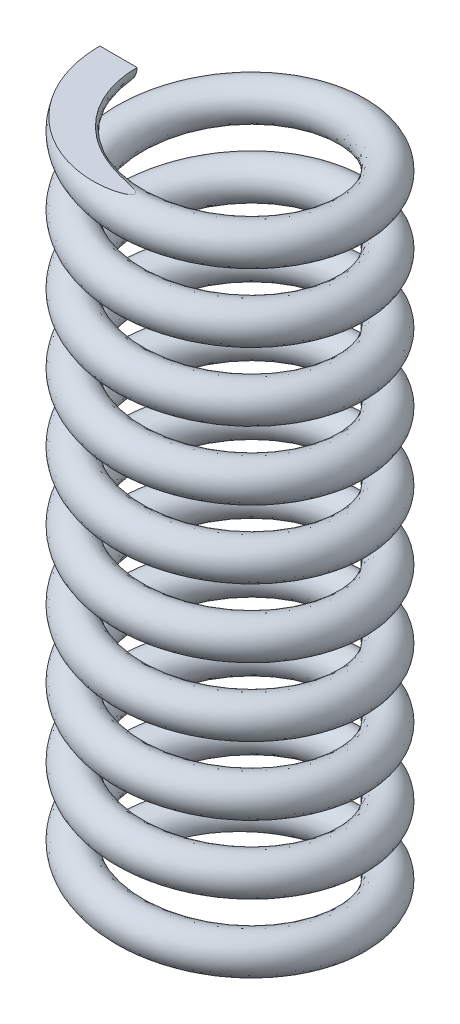
SolidWorks part; units mm, degrees
ref_plane "Front Plane" through (0, 0, 0) normal (0, 0, 1) x (1, 0, 0)
ref_plane "Top Plane" through (0, 0, 0) normal (0, 1, 0) x (1, 0, 0)
ref_plane "Right Plane" through (0, 0, 0) normal (1, 0, 0) x (0, 0, -1)
sketch "Sketch3" plane through (0, 0, 0) normal (0, 1, 0) x (1, 0, 0)
  circle A0 centre (0, 0) radius 30
  dimension "D1" = 60
curve "Helix/Spiral1" pitch 18.3642 height 183.642 turns 10
sketch "Sketch4" plane through (0, 0, 0) normal (0, 0, 1) x (1, 0, 0)
  circle A0 centre (-30, 0) radius 5
  spline S0 degree 3 poles (-30, 0) (-30, 0.2512) (-29.3277, 0.7561) (-26.3694, 1.5114) (-21.6579, 2.2672) (-15.5065, 3.0229) (-8.3241, 3.7786) (-0.5883, 4.5344) (7.1867, 5.2901) (14.4838, 6.0458) (20.8179, 6.8016) (25.768, 7.5573) (29.0049, 8.313) (30.3133, 9.0687) (29.6064, 9.8245) (26.9311, 10.5802) (22.4653, 11.3359) (16.5058, 12.0917) (9.449, 12.8474) (1.7639, 13.6031) (-6.0384, 14.3588) (-13.4393, 15.1146) (-19.9467, 15.8703) (-25.1279, 16.626) (-28.6384, 17.3818) (-30.2449, 18.1375) (-29.8406, 18.8932) (-27.4523, 19.6489) (-23.2388, 20.4047) (-17.4803, 21.1604) (-10.5596, 21.9161) (-2.9369, 22.6719) (4.8811, 23.4276) (12.3746, 24.1833) (19.0454, 24.939) (24.4499, 25.6948) (28.2289, 26.4505) (30.131, 27.2062) (30.0299, 27.962) (27.9322, 28.7177) (23.9775, 29.4734) (18.4286, 30.2291) (11.6544, 30.9849) (4.1054, 31.7406) (-3.7165, 32.4963) (-11.2914, 33.252) (-18.1155, 34.0078) (-23.7352, 34.7635) (-27.7769, 35.5192) (-29.9718, 36.275) (-30.174, 37.0307) (-28.3701, 37.7864) (-24.68, 38.5421) (-19.3491, 39.2979) (-12.7317, 40.0536) (-5.2678, 40.8093) (2.5463, 41.5651) (10.1911, 42.3208) (17.1583, 43.0765) (22.9848, 43.8322) (27.2831, 44.588) (29.7675, 45.3437) (30.2728, 46.0994) (28.7654, 46.8552) (25.3455, 47.6109) (20.2405, 48.3666) (13.7898, 49.1223) (6.4223, 49.8781) (-1.3722, 50.6338) (-9.0755, 51.3895) (-16.1754, 52.1453) (-22.1998, 52.901) (-26.7483, 53.6567) (-29.5184, 54.4124) (-30.326, 55.1682) (-29.1173, 55.9239) (-25.9728, 56.6796) (-21.1015, 57.4354) (-14.8272, 58.1911) (-7.5671, 58.9468) (0.1961, 59.7025) (7.9462, 60.4583) (15.1681, 61.214) (21.3815, 61.9697) (26.1733, 62.7255) (29.225, 63.4812) (30.3336, 64.2369) (29.4255, 64.9926) (26.5611, 65.7484) (21.9307, 66.5041) (15.8422, 67.2598) (8.7005, 68.0156) (0.9803, 68.7713) (-6.805, 69.527) (-14.138, 70.2827) (-20.5309, 71.0385) (-25.5589, 71.7942) (-28.8875, 72.5499) (-30.2956, 73.3057) (-29.6894, 74.0614) (-27.1094, 74.8171) (-22.7269, 75.5728) (-16.8335, 76.3286) (-9.8208, 77.0843) (-2.1553, 77.84) (5.6536, 78.5958) (13.0866, 79.3515) (19.6495, 80.1072) (24.906, 80.8629) (28.5067, 81.6187) (30.212, 82.3744) (29.9087, 83.1301) (27.6169, 83.8859) (23.489, 84.6416) (17.7994, 85.3973) (10.9264, 86.153) (3.327, 86.9088) (-4.4937, 87.6645) (-12.0155, 88.4202) (-18.7385, 89.176) (-24.2157, 89.9317) (-28.0829, 90.6874) (-30.083, 91.4431) (-30.083, 92.1989) (-28.0829, 92.9546) (-24.2157, 93.7103) (-18.7385, 94.466) (-12.0155, 95.2218) (-4.4937, 95.9775) (3.327, 96.7332) (10.9264, 97.489) (17.7994, 98.2447) (23.489, 99.0004) (27.6169, 99.7561) (29.9087, 100.5119) (30.212, 101.2676) (28.5067, 102.0233) (24.906, 102.7791) (19.6495, 103.5348) (13.0866, 104.2905) (5.6536, 105.0462) (-2.1553, 105.802) (-9.8208, 106.5577) (-16.8335, 107.3134) (-22.7269, 108.0692) (-27.1094, 108.8249) (-29.6894, 109.5806) (-30.2956, 110.3363) (-28.8875, 111.0921) (-25.5589, 111.8478) (-20.5309, 112.6035) (-14.138, 113.3593) (-6.805, 114.115) (0.9803, 114.8707) (8.7005, 115.6264) (15.8422, 116.3822) (21.9307, 117.1379) (26.5611, 117.8936) (29.4255, 118.6494) (30.3336, 119.4051) (29.225, 120.1608) (26.1733, 120.9165) (21.3815, 121.6723) (15.1681, 122.428) (7.9462, 123.1837) (0.1961, 123.9395) (-7.5671, 124.6952) (-14.8272, 125.4509) (-21.1015, 126.2066) (-25.9728, 126.9624) (-29.1173, 127.7181) (-30.326, 128.4738) (-29.5184, 129.2296) (-26.7483, 129.9853) (-22.1998, 130.741) (-16.1754, 131.4967) (-9.0755, 132.2525) (-1.3722, 133.0082) (6.4223, 133.7639) (13.7898, 134.5197) (20.2405, 135.2754) (25.3455, 136.0311) (28.7654, 136.7868) (30.2728, 137.5426) (29.7675, 138.2983) (27.2831, 139.054) (22.9848, 139.8098) (17.1583, 140.5655) (10.1911, 141.3212) (2.5463, 142.0769) (-5.2678, 142.8327) (-12.7317, 143.5884) (-19.3491, 144.3441) (-24.68, 145.0999) (-28.3701, 145.8556) (-30.174, 146.6113) (-29.9718, 147.367) (-27.7769, 148.1228) (-23.7352, 148.8785) (-18.1155, 149.6342) (-11.2914, 150.39) (-3.7165, 151.1457) (4.1054, 151.9014) (11.6544, 152.6571) (18.4286, 153.4129) (23.9775, 154.1686) (27.9322, 154.9243) (30.0299, 155.68) (30.131, 156.4358) (28.2289, 157.1915) (24.4499, 157.9472) (19.0454, 158.703) (12.3746, 159.4587) (4.8811, 160.2144) (-2.9369, 160.9701) (-10.5596, 161.7259) (-17.4803, 162.4816) (-23.2388, 163.2373) (-27.4523, 163.9931) (-29.8406, 164.7488) (-30.2449, 165.5045) (-28.6384, 166.2602) (-25.1279, 167.016) (-19.9467, 167.7717) (-13.4393, 168.5274) (-6.0384, 169.2832) (1.7639, 170.0389) (9.449, 170.7946) (16.5058, 171.5503) (22.4653, 172.3061) (26.9311, 173.0618) (29.6064, 173.8175) (30.3133, 174.5733) (29.0049, 175.329) (25.768, 176.0847) (20.8179, 176.8404) (14.4838, 177.5962) (7.1867, 178.3519) (-0.5883, 179.1076) (-8.3241, 179.8634) (-15.5065, 180.6191) (-21.6579, 181.3748) (-26.3694, 182.1306) (-29.3277, 182.8859) (-30, 183.3908) (-30, 183.642) knots 0 0 0 0 0.004115 0.00823 0.012346 0.016461 0.020576 0.024691 0.028807 0.032922 0.037037 0.041152 0.045267 0.049383 0.053498 0.057613 0.061728 0.065844 0.069959 0.074074 0.078189 0.082305 0.08642 0.090535 0.09465 0.098765 0.102881 0.106996 0.111111 0.115226 0.119342 0.123457 0.127572 0.131687 0.135802 0.139918 0.144033 0.148148 0.152263 0.156379 0.160494 0.164609 0.168724 0.17284 0.176955 0.18107 0.185185 0.1893 0.193416 0.197531 0.201646 0.205761 0.209877 0.213992 0.218107 0.222222 0.226337 0.230453 0.234568 0.238683 0.242798 0.246914 0.251029 0.255144 0.259259 0.263374 0.26749 0.271605 0.27572 0.279835 0.283951 0.288066 0.292181 0.296296 0.300412 0.304527 0.308642 0.312757 0.316872 0.320988 0.325103 0.329218 0.333333 0.337449 0.341564 0.345679 0.349794 0.353909 0.358025 0.36214 0.366255 0.37037 0.374486 0.378601 0.382716 0.386831 0.390947 0.395062 0.399177 0.403292 0.407407 0.411523 0.415638 0.419753 0.423868 0.427984 0.432099 0.436214 0.440329 0.444444 0.44856 0.452675 0.45679 0.460905 0.465021 0.469136 0.473251 0.477366 0.481481 0.485597 0.489712 0.493827 0.497942 0.502058 0.506173 0.510288 0.514403 0.518519 0.522634 0.526749 0.530864 0.534979 0.539095 0.54321 0.547325 0.55144 0.555556 0.559671 0.563786 0.567901 0.572016 0.576132 0.580247 0.584362 0.588477 0.592593 0.596708 0.600823 0.604938 0.609053 0.613169 0.617284 0.621399 0.625514 0.62963 0.633745 0.63786 0.641975 0.646091 0.650206 0.654321 0.658436 0.662551 0.666667 0.670782 0.674897 0.679012 0.683128 0.687243 0.691358 0.695473 0.699588 0.703704 0.707819 0.711934 0.716049 0.720165 0.72428 0.728395 0.73251 0.736626 0.740741 0.744856 0.748971 0.753086 0.757202 0.761317 0.765432 0.769547 0.773663 0.777778 0.781893 0.786008 0.790123 0.794239 0.798354 0.802469 0.806584 0.8107 0.814815 0.81893 0.823045 0.82716 0.831276 0.835391 0.839506 0.843621 0.847737 0.851852 0.855967 0.860082 0.864198 0.868313 0.872428 0.876543 0.880658 0.884774 0.888889 0.893004 0.897119 0.901235 0.90535 0.909465 0.91358 0.917695 0.921811 0.925926 0.930041 0.934156 0.938272 0.942387 0.946502 0.950617 0.954733 0.958848 0.962963 0.967078 0.971193 0.975309 0.979424 0.983539 0.987654 0.99177 0.995885 1 1 1 1 construction
  dimension "D1" = 10
sweep "Sweep1" add profiles "Sketch4" path "Helix/Spiral1"
sketch "Sketch5" plane through (0, 0, 0) normal (0, 0, 1) x (1, 0, 0)
  line L1 (-78.8748, 0) -> (92.4962, 0)
  line L2 (-78.8748, 0) -> (-78.8748, -33.3187)
  line L3 (-78.8748, -33.3187) -> (92.4962, -33.3187)
  line L4 (92.4962, 0) -> (92.4962, -33.3187)
extrude "Cut-Extrude1" cut sketch "Sketch5" against normal blind 50.8
sketch "Sketch6" plane through (0, 0, 0) normal (0, 0, -1) x (-1, 0, 0)
  line L0 (50, 183.642) -> (94.2824, 183.642) construction
  line L2 (94.2824, 183.642) -> (-92.0356, 183.642)
  line L3 (94.2824, 183.642) -> (94.2824, 218.3874)
  line L4 (94.2824, 218.3874) -> (-92.0356, 218.3874)
  line L5 (-92.0356, 183.642) -> (-92.0356, 218.3874)
extrude "Cut-Extrude2" cut sketch "Sketch6" against normal blind 63.5
